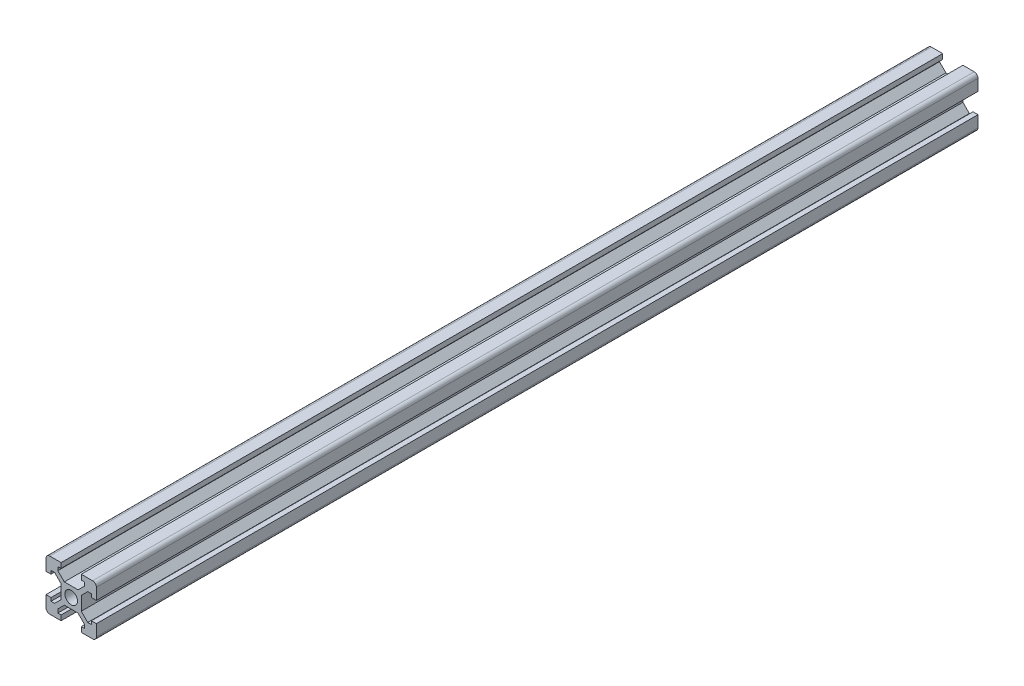
SolidWorks part; units mm, degrees
material "1060 Сплав"
ref_plane "Top" through (0, 0, 0) normal (0, 0, 1) x (1, 0, 0)
ref_plane "Сверху" through (0, 0, 0) normal (0, 1, 0) x (1, 0, 0)
ref_plane "Справа" through (0, 0, 0) normal (1, 0, 0) x (0, 0, -1)
sketch "Эскиз1" plane through (0, 0, 0) normal (0, 0, 1) x (1, 0, 0)
  line L0 (14, 20) -> (20, 20)
  line L1 (0, 0) -> (6, 0)
  line L2 (0, 0) -> (0, 6)
  line L3 (0, 20) -> (6, 20)
  line L4 (20, 0) -> (20, 6)
  line L5 (0, 14) -> (0, 20)
  line L6 (14, 0) -> (20, 0)
  line L7 (20, 14) -> (20, 20)
  line L8 (0, 0) -> (35355.3391, 35355.3391) construction
  line L9 (0, 20) -> (35355.3391, -35335.3391) construction
  line L22 (0, 14) -> (2, 14)
  line L23 (2, 14) -> (2, 15.3)
  line L24 (2, 15.3) -> (3.4272, 15.3)
  line L25 (3.4272, 15.3) -> (6, 12.7272)
  line L26 (6, 12.7272) -> (6, 7.2728)
  line L27 (6, 7.2728) -> (3.4272, 4.7)
  line L28 (3.4272, 4.7) -> (2, 4.7)
  line L29 (2, 4.7) -> (2, 6)
  line L30 (2, 6) -> (0, 6)
  line L31 (6, 0) -> (6, 2)
  line L32 (6, 2) -> (4.7, 2)
  line L33 (4.7, 2) -> (4.7, 3.4272)
  line L34 (4.7, 3.4272) -> (7.2728, 6)
  line L35 (7.2728, 6) -> (12.684, 6)
  line L36 (12.684, 6) -> (15.3, 3.4272)
  line L37 (15.3, 3.4272) -> (15.3, 2)
  line L38 (15.3, 2) -> (14, 2)
  line L39 (14, 2) -> (14, 0)
  line L40 (20, 6) -> (18, 6)
  line L41 (18, 6) -> (18, 4.7)
  line L42 (18, 4.7) -> (16.5728, 4.7)
  line L43 (16.5728, 4.7) -> (14, 7.2728)
  line L44 (14, 7.2728) -> (14, 12.7272)
  line L45 (14, 12.7272) -> (16.5728, 15.3)
  line L46 (16.5728, 15.3) -> (18, 15.3)
  line L47 (18, 15.3) -> (18, 14)
  line L48 (18, 14) -> (20, 14)
  line L49 (6, 20) -> (6, 18)
  line L50 (6, 18) -> (4.7, 18)
  line L51 (4.7, 18) -> (4.7, 16.5728)
  line L52 (4.7, 16.5728) -> (7.2728, 14)
  line L53 (7.2728, 14) -> (12.7272, 14)
  line L54 (12.7272, 14) -> (15.3, 16.5728)
  line L55 (15.3, 16.5728) -> (15.3, 18)
  line L56 (15.3, 18) -> (14, 18)
  line L57 (14, 18) -> (14, 20)
  circle A0 centre (10, 10) radius 2.5
extrude "Бобышка-Вытянуть1" add sketch "Эскиз1" along normal blind 350
fillet "Скругление1" radius 1.5 4 edges at (0, 20, 175) (20, 20, 175) (20, 0, 175) (0, 0, 175)
